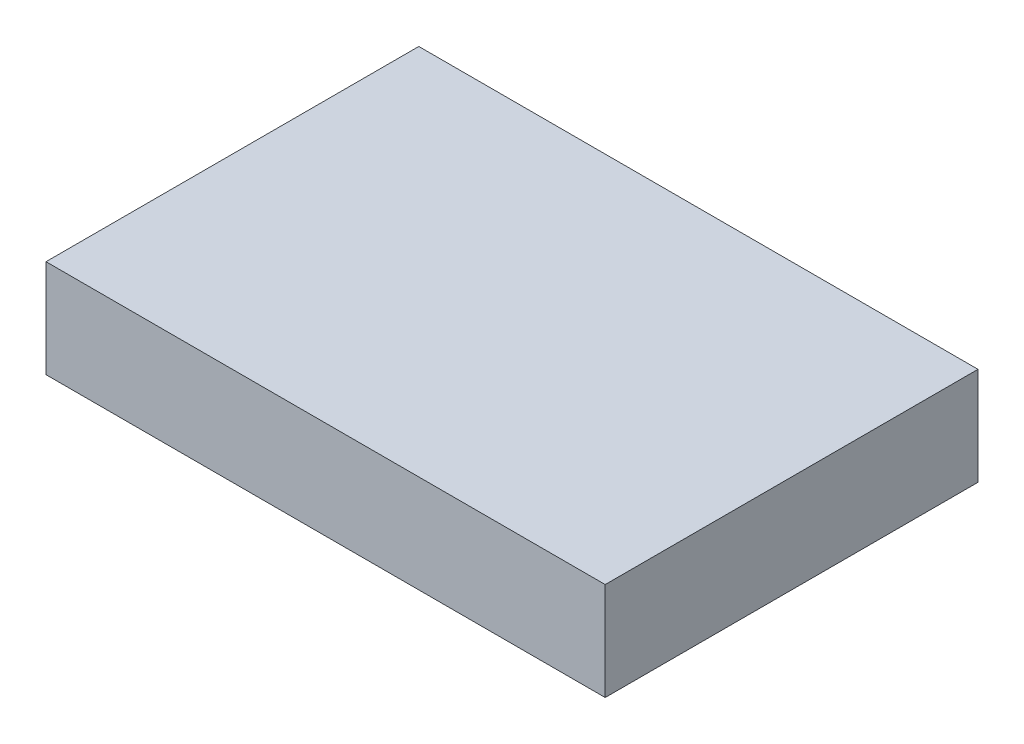
SolidWorks part; units mm, degrees
ref_plane "Front Plane" through (0, 0, 0) normal (0, 0, 1) x (1, 0, 0)
ref_plane "Top Plane" through (0, 0, 0) normal (0, 1, 0) x (1, 0, 0)
ref_plane "Right Plane" through (0, 0, 0) normal (1, 0, 0) x (0, 0, -1)
sketch "Sketch1" plane through (0, 0, 0) normal (0, 1, 0) x (1, 0, 0)
  line L1 (3, 2) -> (-3, 2)
  line L2 (3, 2) -> (3, -2)
  line L3 (3, -2) -> (-3, -2)
  line L4 (-3, 2) -> (-3, -2)
  line L5 (3, 2) -> (-3, -2) construction
  line L6 (3, -2) -> (-3, 2) construction
  point P0 (0, 0)
  dimension "D1" = 4
  dimension "D2" = 6
extrude "Boss-Extrude1" add sketch "Sketch1" along normal blind 1.05
